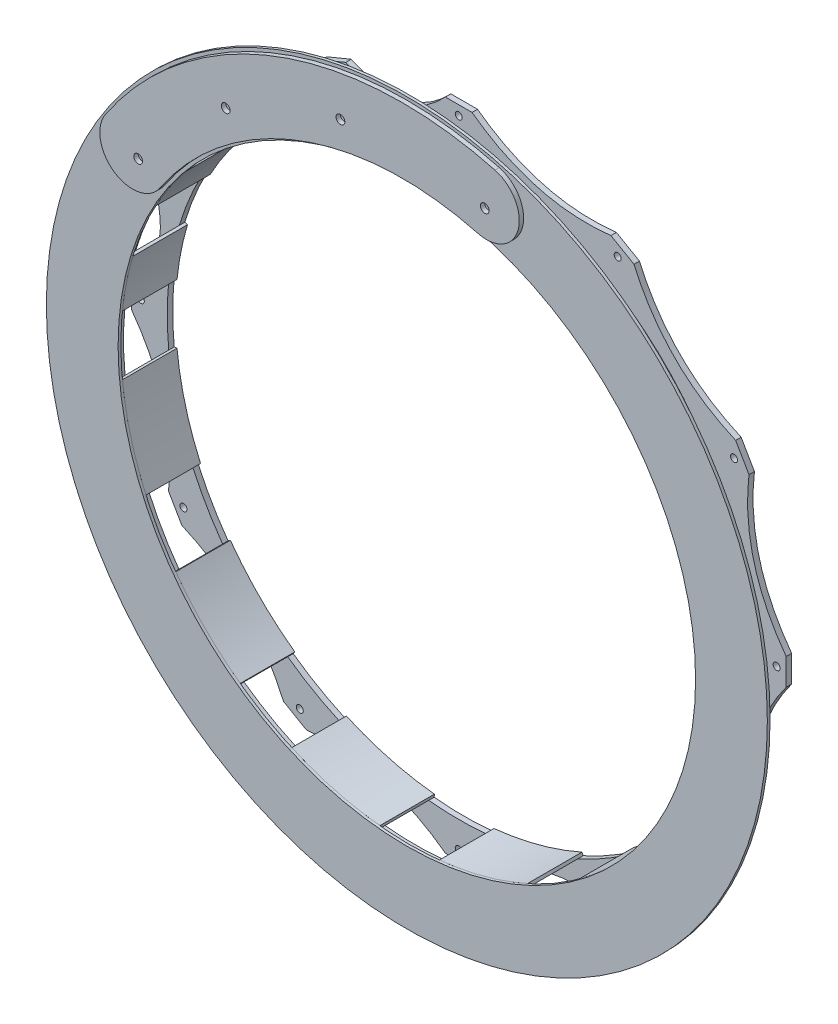
SolidWorks part; units mm, degrees
material "Maple"
ref_plane "Wasteboard" through (0, 0, 0) normal (0, 0, 1) x (1, 0, 0)
ref_plane "Left-Right" through (0, 0, 0) normal (0, 1, 0) x (1, 0, 0)
ref_plane "Front-Back" through (0, 0, 0) normal (1, 0, 0) x (0, 0, -1)
sketch "Sketch2" plane through (0, 0, 0) normal (0, 0, 1) x (1, 0, 0)
  line L0 (0, 0) -> (0, 50000) construction
  circle A0 centre (0, 0) radius 192.8812 construction
  circle A1 centre (0, 0) radius 209.55 construction
  circle A2 centre (0, 0) radius 172.72 construction
  circle A3 centre (0, 0) radius 252.73 construction
  circle A4 centre (0, 0) radius 184.785 construction
  circle A5 centre (0, 0) radius 190.5
  circle A6 centre (0, 0) radius 169.4688
  circle A7 centre (0, 0) radius 194.31 construction
  circle A8 centre (0, 184.785) radius 9.525 construction
  point P14 (0, 172.72)
  point P15 (0, 169.4688)
  point P16 (0, 175.26)
  dimension "D1" = 385.7625
  dimension "D2" = 419.1
  dimension "D3" = 2.54
  dimension "D4" = 505.46
  dimension "D5" = 369.57
  dimension "D6" = 381
  dimension "D7" = 3.2512
  dimension "D8" = 388.62
  dimension "D9" = 19.05
sketch "Sketch4" plane through (0, 0, 0) normal (0, 0, 1) x (1, 0, 0)
  line L0 (92.3925, 160.0285) -> (0, 184.785) construction
  line L1 (46.1963, 172.4068) -> (-12894.756, -48123.8846) construction
  line L2 (-7.7353, 190.3429) -> (7.7353, 190.3429)
  line L6 (-160.9741, -101.8704) -> (-168.7094, -88.4724)
  line L7 (-88.4724, -168.7094) -> (-101.8704, -160.9741)
  line L8 (7.7353, -190.3429) -> (-7.7353, -190.3429)
  line L9 (101.8704, -160.9741) -> (88.4724, -168.7094)
  line L10 (168.7094, -88.4724) -> (160.9741, -101.8704)
  line L11 (190.3429, 7.7353) -> (190.3429, -7.7353)
  line L12 (160.9741, 101.8704) -> (168.7094, 88.4724)
  line L13 (88.4724, 168.7094) -> (101.8704, 160.9741)
  line L14 (-101.8704, 160.9741) -> (-88.4724, 168.7094) [skipped]
  line L15 (-168.7094, 88.4724) -> (-160.9741, 101.8704) [skipped]
  line L16 (-79.9876, 172.8937) -> (-65.6945, 178.8141)
  line L17 (-70.7142, 170.7191) -> (0, 184.785) construction
  line L18 (-35.3571, 177.752) -> (9719.159, -48861.512) construction
  line L19 (-140.0625, 129.123) -> (-129.123, 140.0625)
  line L20 (-178.8141, 65.6945) -> (-172.8937, 79.9876)
  line L21 (-190.3429, -7.7353) -> (-190.3429, 7.7353)
  line L23 (-172.8937, -79.9876) -> (-178.8141, -65.6945) [skipped]
  line L24 (-190.3429, -7.7353) -> (-190.3429, 7.7353) [skipped]
  circle A0 centre (0, 184.785) radius 3.175 construction
  circle A1 centre (0, 184.785) radius 9.525 construction
  circle A2 centre (0, 184.785) radius 9.525 construction
  circle A3 centre (0, 0) radius 177.6413 construction
  circle A4 centre (0, 0) radius 190.5 construction
  circle A5 centre (0, 0) radius 184.785 construction
  circle A6 centre (0, 0) radius 169.4688 construction
  circle A7 centre (0, 0) radius 169.4688
  circle A8 centre (92.3925, 160.0285) radius 9.525 construction
  circle A9 centre (0, 0) radius 192.8812 construction
  circle A10 centre (0, 184.785) radius 2.032
  circle A14 centre (-160.0285, -92.3925) radius 2.032
  circle A15 centre (-92.3925, -160.0285) radius 2.032
  circle A16 centre (0, -184.785) radius 2.032
  circle A17 centre (92.3925, -160.0285) radius 2.032
  circle A18 centre (160.0285, -92.3925) radius 2.032
  circle A19 centre (184.785, 0) radius 2.032
  circle A20 centre (160.0285, 92.3925) radius 2.032
  circle A21 centre (92.3925, 160.0285) radius 2.032
  circle A22 centre (-160.0285, 92.3925) radius 2.032 [skipped]
  circle A23 centre (-92.3925, 160.0285) radius 2.032 [skipped]
  circle A24 centre (-70.7142, 170.7191) radius 9.525 construction
  circle A25 centre (-130.6627, 130.6627) radius 9.525 construction
  circle A26 centre (-170.7191, 70.7142) radius 9.525 construction
  circle A27 centre (-184.785, 0) radius 9.525 construction
  circle A28 centre (-70.7142, 170.7191) radius 2.032
  circle A29 centre (-130.6627, 130.6627) radius 2.032
  circle A30 centre (-170.7191, 70.7142) radius 2.032
  circle A31 centre (-184.785, 0) radius 2.032
  circle A32 centre (-184.785, 0) radius 2.032 [skipped]
  spline S0 degree 2 poles (7.7353, 190.3429) (43.85, 163.6504) (88.4724, 168.7094) knots 0 0 0 1 1 1
  spline S1 degree 2 poles (-65.6945, 178.8141) (-32.5972, 163.8774) (-7.7353, 190.3429) knots 0 0 0 1 1 1
  spline S2 degree 2 poles (-129.123, 140.0625) (-92.8291, 138.9285) (-79.9876, 172.8937) knots 0 0 0 1 1 1
  spline S3 degree 2 poles (-172.8937, 79.9876) (-138.9285, 92.8291) (-140.0625, 129.123) knots 0 0 0 1 1 1
  spline S4 degree 2 poles (-168.7094, -88.4724) (-163.6504, -43.85) (-190.3429, -7.7353) knots 0 0 0 1 1 1
  spline S5 degree 2 poles (-101.8704, -160.9741) (-119.8004, -119.8004) (-160.9741, -101.8704) knots 0 0 0 1 1 1
  spline S6 degree 2 poles (-7.7353, -190.3429) (-43.85, -163.6504) (-88.4724, -168.7094) knots 0 0 0 1 1 1
  spline S7 degree 2 poles (88.4724, -168.7094) (43.85, -163.6504) (7.7353, -190.3429) knots 0 0 0 1 1 1
  spline S8 degree 2 poles (160.9741, -101.8704) (119.8004, -119.8004) (101.8704, -160.9741) knots 0 0 0 1 1 1
  spline S9 degree 2 poles (190.3429, -7.7353) (163.6504, -43.85) (168.7094, -88.4724) knots 0 0 0 1 1 1
  spline S10 degree 2 poles (168.7094, 88.4724) (163.6504, 43.85) (190.3429, 7.7353) knots 0 0 0 1 1 1
  spline S11 degree 2 poles (101.8704, 160.9741) (119.8004, 119.8004) (160.9741, 101.8704) knots 0 0 0 1 1 1
  spline S12 degree 2 poles (-190.3429, 7.7353) (-163.8774, 32.5972) (-178.8141, 65.6945) knots 0 0 0 1 1 1
  point P6 (0, 0)
  point P18 (0, 0)
  point P19 (0, 0)
  point P21 (0, 0)
  point P24 (45.9769, 171.5883)
  point P29 (46.1963, 172.4068)
  point P31 (-7.7353, 190.3429)
  point P33 (-79.9876, 172.8937)
  point P34 (-65.6945, 178.8141)
  point P45 (0, 0)
  point P48 (-34.6561, 174.2279)
  point P103 (0, 0)
  point P112 (-35.3571, 177.752)
  point P123 (0, 0)
  point P126 (0, 0)
  dimension "D1" = 6.35
  dimension "D2" = 19.05
  dimension "D3" = 15.24
  dimension "D6" = 4.064
  dimension "D7" = 12
  dimension "D4" = 2
  dimension "D5" = 2
  dimension "D8" = 5
  dimension "D9" = 5
extrude "Boss-Extrude1" add sketch "Sketch4" along normal blind 3.175
ref_plane "Plane1" through (0, 0, 28.575) normal (0, 0, 1) x (1, 0, 0)
sketch "Sketch5" plane through (0, 0, 28.575) normal (0, 0, 1) x (1, 0, 0)
  line L13 (-129.123, 140.0625) -> (-140.0625, 129.123)
  line L14 (-65.6945, 178.8141) -> (-79.9876, 172.8937)
  line L15 (7.7353, 190.3429) -> (-7.7353, 190.3429)
  line L16 (101.8704, 160.9741) -> (88.4724, 168.7094)
  line L17 (168.7094, 88.4724) -> (160.9741, 101.8704)
  line L18 (190.3429, -7.7353) -> (190.3429, 7.7353)
  line L19 (160.9741, -101.8704) -> (168.7094, -88.4724)
  line L20 (88.4724, -168.7094) -> (101.8704, -160.9741)
  line L21 (-7.7353, -190.3429) -> (7.7353, -190.3429)
  line L22 (-101.8704, -160.9741) -> (-88.4724, -168.7094)
  line L23 (-168.7094, -88.4724) -> (-160.9741, -101.8704)
  line L24 (-190.3429, 7.7353) -> (-190.3429, -7.7353)
  line L25 (-172.8937, 79.9876) -> (-178.8141, 65.6945)
  line L26 (-129.123, 140.0625) -> (-140.0625, 129.123)
  line L27 (-65.6945, 178.8141) -> (-79.9876, 172.8937)
  line L28 (7.7353, 190.3429) -> (-7.7353, 190.3429)
  line L29 (101.8704, 160.9741) -> (88.4724, 168.7094)
  line L30 (168.7094, 88.4724) -> (160.9741, 101.8704)
  line L31 (190.3429, -7.7353) -> (190.3429, 7.7353)
  line L32 (160.9741, -101.8704) -> (168.7094, -88.4724)
  line L33 (88.4724, -168.7094) -> (101.8704, -160.9741)
  line L34 (-7.7353, -190.3429) -> (7.7353, -190.3429)
  line L35 (-101.8704, -160.9741) -> (-88.4724, -168.7094)
  line L36 (-168.7094, -88.4724) -> (-160.9741, -101.8704)
  line L37 (-190.3429, 7.7353) -> (-190.3429, -7.7353)
  line L38 (-172.8937, 79.9876) -> (-178.8141, 65.6945)
  circle A1 centre (0, 0) radius 169.4688
  circle A2 centre (0, 0) radius 169.4688
  circle A3 centre (0, 184.785) radius 2.032
  circle A4 centre (0, 184.785) radius 2.032
  circle A5 centre (-160.0285, -92.3925) radius 2.032
  circle A6 centre (-160.0285, -92.3925) radius 2.032
  circle A7 centre (-70.7142, 170.7191) radius 2.032
  circle A8 centre (-70.7142, 170.7191) radius 2.032
  circle A9 centre (92.3925, -160.0285) radius 2.032
  circle A10 centre (92.3925, -160.0285) radius 2.032
  circle A11 centre (0, -184.785) radius 2.032
  circle A12 centre (0, -184.785) radius 2.032
  circle A13 centre (-92.3925, -160.0285) radius 2.032
  circle A14 centre (-92.3925, -160.0285) radius 2.032
  circle A15 centre (184.785, 0) radius 2.032
  circle A16 centre (184.785, 0) radius 2.032
  circle A17 centre (160.0285, -92.3925) radius 2.032
  circle A18 centre (160.0285, -92.3925) radius 2.032
  circle A19 centre (92.3925, 160.0285) radius 2.032
  circle A20 centre (92.3925, 160.0285) radius 2.032
  circle A21 centre (160.0285, 92.3925) radius 2.032
  circle A22 centre (160.0285, 92.3925) radius 2.032
  circle A23 centre (-184.785, 0) radius 2.032
  circle A24 centre (-184.785, 0) radius 2.032
  circle A25 centre (-170.7191, 70.7142) radius 2.032
  circle A26 centre (-170.7191, 70.7142) radius 2.032
  circle A27 centre (-130.6627, 130.6627) radius 2.032
  circle A28 centre (-130.6627, 130.6627) radius 2.032
  parabola Q13 (-140.0625, 129.123) -> (-172.8937, 79.9876) focus (-164.8995, 110.1823) apex (-147.7033, 98.6922)
  parabola Q14 (-79.9876, 172.8937) -> (-129.123, 140.0625) focus (-110.1823, 164.8995) apex (-98.6922, 147.7033)
  parabola Q15 (-7.7353, 190.3429) -> (-65.6945, 178.8141) focus (-38.6909, 194.5123) apex (-34.6561, 174.2279)
  parabola Q16 (88.4724, 168.7094) -> (7.7353, 190.3429) focus (59.7292, 222.9123) apex (45.9769, 171.5883)
  parabola Q17 (160.9741, 101.8704) -> (101.8704, 160.9741) focus (163.1831, 163.1831) apex (125.6113, 125.6113)
  parabola Q18 (190.3429, 7.7353) -> (168.7094, 88.4724) focus (222.9123, 59.7292) apex (171.5883, 45.9769)
  parabola Q19 (168.7094, -88.4724) -> (190.3429, -7.7353) focus (222.9123, -59.7292) apex (171.5883, -45.9769)
  parabola Q20 (101.8704, -160.9741) -> (160.9741, -101.8704) focus (163.1831, -163.1831) apex (125.6113, -125.6113)
  parabola Q21 (7.7353, -190.3429) -> (88.4724, -168.7094) focus (59.7292, -222.9123) apex (45.9769, -171.5883)
  parabola Q22 (-88.4724, -168.7094) -> (-7.7353, -190.3429) focus (-59.7292, -222.9123) apex (-45.9769, -171.5883)
  parabola Q23 (-160.9741, -101.8704) -> (-101.8704, -160.9741) focus (-163.1831, -163.1831) apex (-125.6113, -125.6113)
  parabola Q24 (-190.3429, -7.7353) -> (-168.7094, -88.4724) focus (-222.9123, -59.7292) apex (-171.5883, -45.9769)
  parabola Q25 (-178.8141, 65.6945) -> (-190.3429, 7.7353) focus (-194.5123, 38.6909) apex (-174.2279, 34.6561)
  parabola Q26 (-140.0625, 129.123) -> (-172.8937, 79.9876) focus (-164.8995, 110.1823) apex (-147.7033, 98.6922)
  parabola Q27 (-79.9876, 172.8937) -> (-129.123, 140.0625) focus (-110.1823, 164.8995) apex (-98.6922, 147.7033)
  parabola Q28 (-7.7353, 190.3429) -> (-65.6945, 178.8141) focus (-38.6909, 194.5123) apex (-34.6561, 174.2279)
  parabola Q29 (88.4724, 168.7094) -> (7.7353, 190.3429) focus (59.7292, 222.9123) apex (45.9769, 171.5883)
  parabola Q30 (160.9741, 101.8704) -> (101.8704, 160.9741) focus (163.1831, 163.1831) apex (125.6113, 125.6113)
  parabola Q31 (190.3429, 7.7353) -> (168.7094, 88.4724) focus (222.9123, 59.7292) apex (171.5883, 45.9769)
  parabola Q32 (168.7094, -88.4724) -> (190.3429, -7.7353) focus (222.9123, -59.7292) apex (171.5883, -45.9769)
  parabola Q33 (101.8704, -160.9741) -> (160.9741, -101.8704) focus (163.1831, -163.1831) apex (125.6113, -125.6113)
  parabola Q34 (7.7353, -190.3429) -> (88.4724, -168.7094) focus (59.7292, -222.9123) apex (45.9769, -171.5883)
  parabola Q35 (-88.4724, -168.7094) -> (-7.7353, -190.3429) focus (-59.7292, -222.9123) apex (-45.9769, -171.5883)
  parabola Q36 (-160.9741, -101.8704) -> (-101.8704, -160.9741) focus (-163.1831, -163.1831) apex (-125.6113, -125.6113)
  parabola Q37 (-190.3429, -7.7353) -> (-168.7094, -88.4724) focus (-222.9123, -59.7292) apex (-171.5883, -45.9769)
  parabola Q38 (-178.8141, 65.6945) -> (-190.3429, 7.7353) focus (-194.5123, 38.6909) apex (-174.2279, 34.6561)
  dimension "D1" = 0
  dimension "D2" = 0
  dimension "D3" = 0
  dimension "D4" = 0
  dimension "D5" = 0
  dimension "D6" = 0
  dimension "D7" = 0
  dimension "D8" = 0
  dimension "D9" = 0
  dimension "D10" = 0
  dimension "D11" = 0
  dimension "D12" = 0
  dimension "D13" = 0
  dimension "D14" = 0
  dimension "D15" = 0
extrude "Boss-Extrude2" add sketch "Sketch5" along normal blind 3.175 separate body
sketch "Sketch6" plane through (0, 0, 31.75) normal (0, 0, 1) x (1, 0, 0)
  line L0 (0, 0) -> (5154.6392, 49733.5872) construction
  line L1 (0, 0) -> (20402.7451, 45647.8695) construction
  line L2 (17.471, 168.5658) -> (17.3034, 166.9489)
  line L3 (68.4892, 153.2337) -> (69.1526, 154.7178)
  line L4 (99.4133, 137.2468) -> (98.4596, 135.9303)
  line L5 (135.9303, 98.4596) -> (137.2468, 99.4133)
  line L6 (154.7178, 69.1526) -> (153.2337, 68.4892)
  line L7 (166.9489, 17.3034) -> (168.5658, 17.471)
  line L8 (168.5658, -17.471) -> (166.9489, -17.3034)
  line L9 (153.2337, -68.4892) -> (154.7178, -69.1526)
  line L10 (137.2468, -99.4133) -> (135.9303, -98.4596)
  line L11 (98.4596, -135.9303) -> (99.4133, -137.2468)
  line L12 (69.1526, -154.7178) -> (68.4892, -153.2337)
  line L39 (17.3034, -166.9489) -> (17.471, -168.5658)
  line L40 (-17.471, -168.5658) -> (-17.3034, -166.9489)
  line L41 (-68.4892, -153.2337) -> (-69.1526, -154.7178)
  line L42 (-99.4133, -137.2468) -> (-98.4596, -135.9303)
  line L43 (-135.9303, -98.4596) -> (-137.2468, -99.4133)
  line L44 (-154.7178, -69.1526) -> (-153.2337, -68.4892)
  line L45 (-166.9489, -17.3034) -> (-168.5658, -17.471)
  line L46 (0, 0) -> (68.4892, 153.2337) construction
  line L47 (0, 0) -> (135.9303, 98.4596) construction
  line L48 (0, 0) -> (-5154.6392, 49733.5872) construction
  line L49 (0, 0) -> (-14269.9542, 47920.4383) construction
  line L50 (-47.9023, 160.8624) -> (-48.3662, 162.4204)
  line L51 (-17.3034, 166.9489) -> (-17.471, 168.5658)
  line L52 (-105.8153, 130.2861) -> (-106.8402, 131.5479)
  line L53 (-79.8749, 147.6189) -> (-80.6485, 149.0487)
  line L54 (-147.6189, 79.8749) -> (-149.0487, 80.6485)
  line L55 (-130.2861, 105.8153) -> (-131.5479, 106.8402)
  line L56 (-166.9489, 17.3034) -> (-168.5658, 17.471)
  line L57 (-160.8624, 47.9023) -> (-162.4204, 48.3662)
  line L58 (0, 0) -> (-17.3034, 166.9489) construction
  line L59 (0, 0) -> (-79.8749, 147.6189) construction
  circle A0 centre (92.3925, 160.0285) radius 2.032 construction
  arc A1 (17.471, 168.5658) -> (69.1526, 154.7178) centre (0, 0) cw
  circle A2 centre (0, 0) radius 169.4688 construction
  arc A3 (17.3034, 166.9489) -> (68.4892, 153.2337) centre (0, 0) cw
  arc A4 (99.4133, 137.2468) -> (137.2468, 99.4133) centre (0, 0) cw
  arc A5 (98.4596, 135.9303) -> (135.9303, 98.4596) centre (0, 0) cw
  arc A6 (154.7178, 69.1526) -> (168.5658, 17.471) centre (0, 0) cw
  arc A7 (153.2337, 68.4892) -> (166.9489, 17.3034) centre (0, 0) cw
  arc A8 (168.5658, -17.471) -> (154.7178, -69.1526) centre (0, 0) cw
  arc A9 (166.9489, -17.3034) -> (153.2337, -68.4892) centre (0, 0) cw
  arc A10 (137.2468, -99.4133) -> (99.4133, -137.2468) centre (0, 0) cw
  arc A11 (135.9303, -98.4596) -> (98.4596, -135.9303) centre (0, 0) cw
  arc A12 (69.1526, -154.7178) -> (17.471, -168.5658) centre (0, 0) cw
  arc A13 (68.4892, -153.2337) -> (17.3034, -166.9489) centre (0, 0) cw
  arc A14 (-17.471, -168.5658) -> (-69.1526, -154.7178) centre (0, 0) cw
  arc A15 (-17.3034, -166.9489) -> (-68.4892, -153.2337) centre (0, 0) cw
  arc A16 (-99.4133, -137.2468) -> (-137.2468, -99.4133) centre (0, 0) cw
  arc A17 (-98.4596, -135.9303) -> (-135.9303, -98.4596) centre (0, 0) cw
  arc A18 (-154.7178, -69.1526) -> (-168.5658, -17.471) centre (0, 0) cw
  arc A19 (-153.2337, -68.4892) -> (-166.9489, -17.3034) centre (0, 0) cw
  circle A20 centre (-70.7142, 170.7191) radius 2.032 construction
  arc A21 (-48.3662, 162.4204) -> (-17.471, 168.5658) centre (0, 0) cw
  arc A22 (-47.9023, 160.8624) -> (-17.3034, 166.9489) centre (0, 0) cw
  arc A23 (-106.8402, 131.5479) -> (-80.6485, 149.0487) centre (0, 0) cw
  arc A24 (-105.8153, 130.2861) -> (-79.8749, 147.6189) centre (0, 0) cw
  arc A25 (-149.0487, 80.6485) -> (-131.5479, 106.8402) centre (0, 0) cw
  arc A26 (-147.6189, 79.8749) -> (-130.2861, 105.8153) centre (0, 0) cw
  arc A27 (-168.5658, 17.471) -> (-162.4204, 48.3662) centre (0, 0) cw
  arc A28 (-166.9489, 17.3034) -> (-160.8624, 47.9023) centre (0, 0) cw
  dimension "D3" = 19.05
  dimension "D7" = 19.05
  dimension "D2" = 19.05
  dimension "D4" = 1.6256
  dimension "D6" = 30
  dimension "D8" = 19.05
  dimension "D9" = 1.6256
  dimension "D11" = 22.5
  dimension "D5" = 9
  dimension "D10" = 4
extrude "Boss-Extrude3" add sketch "Sketch6" against normal through all
sketch "Sketch7" plane through (0, 0, 31.75) normal (0, 0, 1) x (1, 0, 0)
  circle A0 centre (0, 0) radius 167.8432
  circle A1 centre (0, 0) radius 209.55
  arc A2 (-166.9489, -17.3034) -> (-153.2337, -68.4892) centre (0, 0) ccw construction
  circle A5 centre (0, 0) radius 209.55 construction
  dimension "D1" = 41.7068
extrude "Boss-Extrude4" add sketch "Sketch7" along normal blind 1.5875 separate body
sketch "Sketch8" plane through (0, 0, 33.3375) normal (0, 0, 1) x (1, 0, 0)
  line L0 (27596.442, 41627.2074) -> (-27909.1744, -41442.8179) construction
  line L1 (-159.6471, 106.6728) -> (-517.5318, -428.9395) construction
  line L2 (-130.6627, 130.6627) -> (-170.7191, 70.7142) construction
  line L3 (-130.6627, 130.6627) -> (-156.9608, 104.8779) construction
  line L4 (-156.9608, 104.8779) -> (-170.7191, 70.7142) construction
  line L5 (-156.9608, 104.8779) -> (-159.6471, 106.6728) construction
  line L6 (-159.6471, 106.6728) -> (-341.4213, -256.8091) construction
  line L7 (-341.4213, -256.8091) -> (-383.66, -228.5861) construction
  line L8 (0, 184.785) -> (92.3925, 160.0285) construction
  line L9 (48.8323, 182.2448) -> (46.1963, 172.4068) construction
  line L10 (-130.6627, 130.6627) -> (-170.7191, 70.7142) construction
  line L11 (-130.6627, 130.6627) -> (-109.2149, 116.3318) construction
  line L12 (-109.2149, 116.3318) -> (-149.2713, 56.3832) construction
  line L13 (-149.2713, 56.3832) -> (-170.7191, 70.7142) construction
  line L14 (-129.2431, 86.3575) -> (-156.8765, 104.8215) construction
  line L15 (0, 209.55) -> (0, 167.7974) construction
  line L16 (0, -200000) -> (0, 250000) construction
  line L20 (-39053.4215, 196334.8081) -> (48737.2234, -245018.5681) construction
  circle A0 centre (-170.7191, 70.7142) radius 2.032 construction
  circle A1 centre (-130.6627, 130.6627) radius 2.032 construction
  circle A2 centre (-170.7191, 70.7142) radius 2.032 construction
  circle A3 centre (-130.6627, 130.6627) radius 2.032 construction
  circle A4 centre (0, 0) radius 190.5 construction
  circle A5 centre (0, 0) radius 209.55 construction
  circle A6 centre (0, 0) radius 184.785 construction
  arc A7 (48.8323, 182.2448) -> (-156.8765, 104.8215) centre (0, 0) ccw construction
  arc A8 (53.7629, 200.6457) -> (-172.716, 115.4051) centre (0, 0) ccw
  arc A9 (43.9018, 163.8439) -> (-141.037, 94.2379) centre (0, 0) ccw
  arc A10 (53.7629, 200.6457) -> (43.9018, 163.8439) centre (48.8323, 182.2448) cw
  arc A11 (-141.037, 94.2379) -> (-172.716, 115.4051) centre (-156.8765, 104.8215) cw
  circle A13 centre (47.8259, 178.4886) radius 2.54
  circle A14 centre (-153.6431, 102.661) radius 2.54
  circle A15 centre (-36.0498, 181.2344) radius 2.54
  circle A16 centre (-102.7427, 153.5885) radius 2.54
  point P30 (-153.6431, 102.661)
  point P44 (-153.6431, 102.661)
  point P45 (47.8259, 178.4886)
  point P52 (0, 0)
  point P54 (0, 0)
  point P58 (0, 0)
  point P60 (0, 0)
  point P61 (0, 0)
  point P62 (0, 0)
  dimension "D4" = 41.7526
  dimension "D5" = 19.05
  dimension "D7" = 5.08
  dimension "D8" = 5.08
  dimension "D9" = 5.08
  dimension "D10" = 5.08
  dimension "D1" = 36.83
  dimension "D2" = 50.8
  dimension "D3" = 406.4
  dimension "D11" = 36.322
  dimension "D6" = 19.05
extrude "Boss-Extrude5" add sketch "Sketch8" along normal blind 2.54 separate body contours A11 A9 A10 A8 A16 A15 A14 A13
